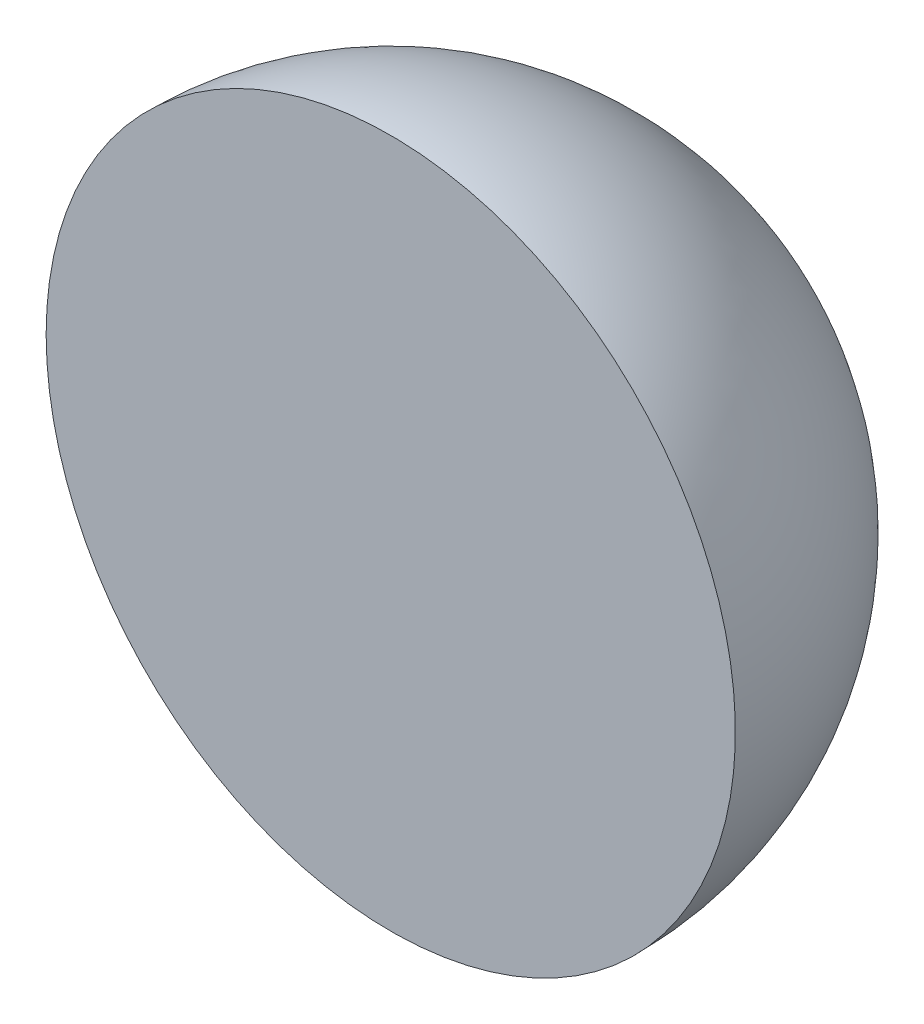
SolidWorks part; units mm, degrees
ref_plane "Front Plane" through (0, 0, 0) normal (0, 0, 1) x (1, 0, 0)
ref_plane "Top Plane" through (0, 0, 0) normal (0, 1, 0) x (1, 0, 0)
ref_plane "Right Plane" through (0, 0, 0) normal (1, 0, 0) x (0, 0, -1)
sketch "Sketch1" plane through (0, 0, 0) normal (0, 0, 1) x (1, 0, 0)
  line L0 (0, 50) -> (0, -50)
  arc A0 (0, 50) -> (0, -50) centre (0, 0) ccw
  dimension "D1" = 100
revolve "Revolve1" add sketch "Sketch1" angle 180 about L0
equation "\"D1@Sketch1\" = 100"
